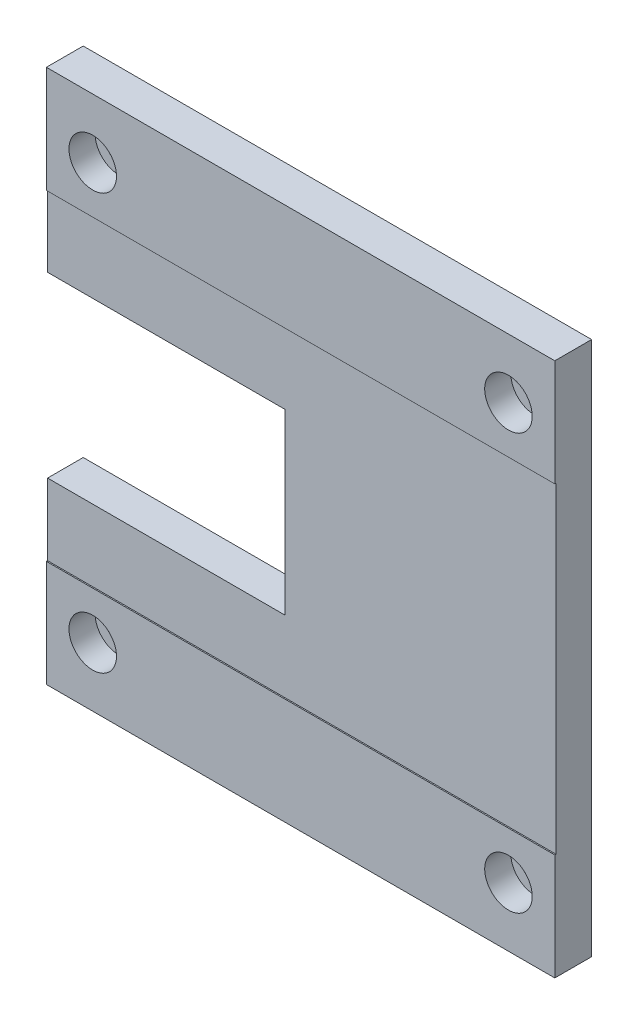
SolidWorks part; units mm, degrees
ref_plane "前视基准面" through (0, 0, 0) normal (0, 0, 1) x (1, 0, 0)
ref_plane "上视基准面" through (0, 0, 0) normal (0, 1, 0) x (1, 0, 0)
ref_plane "右视基准面" through (0, 0, 0) normal (1, 0, 0) x (0, 0, -1)
sketch "草图1" plane through (0, 0, 0) normal (0, 0, 1) x (1, 0, 0)
  line L1 (0, 0) -> (85.6, 0)
  line L2 (0, 0) -> (0, 90)
  line L3 (0, 90) -> (85.6, 90)
  line L4 (85.6, 0) -> (85.6, 90)
  dimension "D1" = 85.6
  dimension "D2" = 90
extrude "凸台-拉伸1" add sketch "草图1" along normal blind 6
sketch "草图2" plane through (0, 0, 6) normal (0, 0, 1) x (1, 0, 0)
  line L0 (0, 90) -> (0, 0) construction
  line L1 (85.6, 90) -> (0, 90)
  line L2 (85.6, 90) -> (85.6, 72.05)
  line L3 (85.6, 72.05) -> (0, 72.05)
  line L4 (0, 90) -> (0, 72.05)
  line L5 (42.8, 0) -> (42.8, 90) construction
  line L6 (0, 0) -> (85.6, 0) construction
  line L7 (42.8, 90) -> (42.8, 45) construction
  line L8 (42.8, 45) -> (71.9817, 45) construction
  line L9 (0, 0) -> (0, 17.95)
  line L10 (85.6, 17.95) -> (0, 17.95)
  line L11 (85.6, 0) -> (0, 0)
  line L12 (85.6, 0) -> (85.6, 17.95)
  dimension "D1" = 54.1
extrude "凸台-拉伸2" add sketch "草图2" along normal blind 0.2
sketch "草图3" plane through (0, 0, 6) normal (0, 0, 1) x (1, 0, 0)
  line L0 (0, 45) -> (112.2735, 45) construction
  line L1 (0, 72.05) -> (0, 17.95) construction
  line L3 (0, 60) -> (40, 60)
  line L4 (0, 60) -> (0, 30)
  line L5 (0, 30) -> (40, 30)
  line L6 (40, 60) -> (40, 30)
  dimension "D1" = 30
  dimension "D2" = 40
extrude "切除-拉伸1" cut sketch "草图3" against normal through all
hole_wizard "M4 六角凹头螺钉的柱形沉头孔1" positions "草图6" profile "草图7" counterbore size "M4" standard "ISO" end condition through all
sketch "草图6" plane through (0, 0, 6.2) normal (0, 0, 1) x (1, 0, 0)
  line L0 (42.8, 90) -> (42.8, 0) construction
  line L1 (85.6, 90) -> (0, 90) construction
  line L2 (0, 0) -> (85.6, 0) construction
  line L3 (42.8, 0) -> (42.8, 45) construction
  line L4 (42.8, 45) -> (-12.8672, 45) construction
  point P0 (77.8, 80)
  point P14 (7.8, 80)
  point P15 (7.8, 10)
  point P16 (77.8, 10)
  dimension "D1" = 70
  dimension "D2" = 70
sketch "草图7" plane through (77.8, 80, 6.2) normal (1, 0, 0) x (0, -1, 0)
  line L0 (0, 0) -> (0, 6.2)
  line L1 (0, 6.2) -> (2.25, 6.2)
  line L3 (2.25, 6.2) -> (2.25, 4.4)
  line L4 (2.25, 4.4) -> (4, 4.4)
  line L5 (4, 4.4) -> (4, 0)
  line L7 (4, 0) -> (0, 0)
  line L11 (0, -6.35) -> (0, 107.95) construction
  dimension "通孔孔直径" = 4.5
  dimension "通孔孔深度" = 6.2
  dimension "柱形沉头孔直径" = 8
  dimension "柱形沉头孔深度" = 4.4
